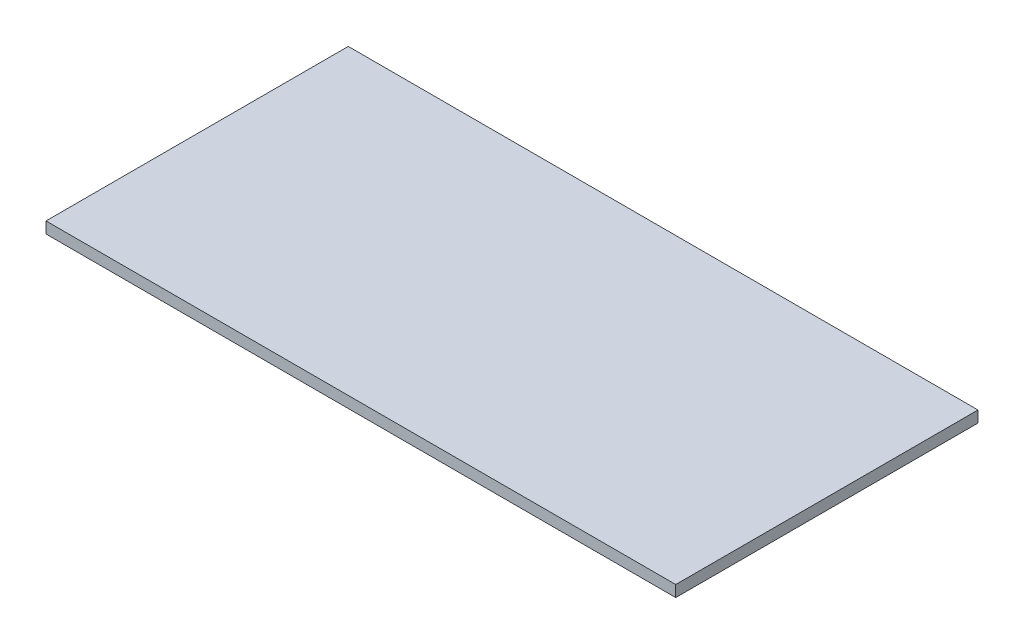
SolidWorks part; units mm, degrees
ref_plane "前视基准面" through (0, 0, 0) normal (0, 0, 1) x (1, 0, 0)
ref_plane "上视基准面" through (0, 0, 0) normal (0, 1, 0) x (1, 0, 0)
ref_plane "右视基准面" through (0, 0, 0) normal (1, 0, 0) x (0, 0, -1)
sketch "草图1" plane through (0, 0, 0) normal (0, 1, 0) x (1, 0, 0)
  line L1 (0, 0) -> (100, 0)
  line L2 (0, 0) -> (0, 48)
  line L3 (0, 48) -> (100, 48)
  line L4 (100, 0) -> (100, 48)
  dimension "D1" = 100
  dimension "D2" = 48
extrude "凸台-拉伸1" add sketch "草图1" along normal blind 1.8
